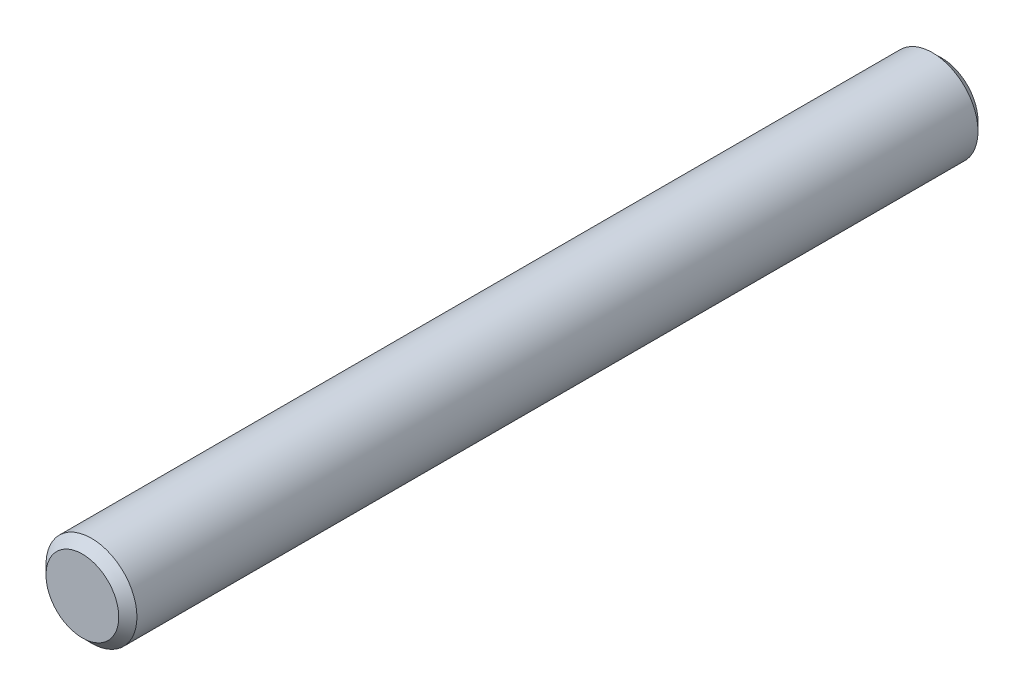
SolidWorks part; units mm, degrees
material "Plain Carbon Steel"
ref_plane "Front" through (0, 0, 0) normal (0, 0, 1) x (1, 0, 0)
ref_plane "Top" through (0, 0, 0) normal (0, 1, 0) x (1, 0, 0)
ref_plane "Right" through (0, 0, 0) normal (1, 0, 0) x (0, 0, -1)
sketch "Sketch1" plane through (0, 0, 0) normal (0, 0, 1) x (1, 0, 0)
  circle A0 centre (0, 0) radius 7.9375
  dimension "Diameter" = 15.875
sketch "Sketch2" plane through (0, 0, 0) normal (1, 0, 0) x (0, 0, -1)
  line L0 (-75, 0) -> (75, 0) construction
  line L1 (-24.2, 7.9375) -> (-24.2, -7.9375) construction
  line L2 (55, 0) -> (-55, 0) construction
  line L3 (24.2, 7.9375) -> (24.2, -7.9375) construction
  line L4 (-75, 7.9375) -> (-75, -7.9375) construction
  line L5 (75, 7.9375) -> (75, -7.9375) construction
  point P3 (-24.2, 0)
  point P8 (0, 0)
  point P9 (24.2, 0)
  point P15 (-75, 0)
  point P18 (75, 0)
  dimension "D1" = 15.875
  dimension "Length" = 150
  dimension "D2" = 50.8
  dimension "D3" = 50.8
sketch "Sketch3" plane through (0, 0, 0) normal (0, 0, 1) x (1, 0, 0)
  circle A0 centre (0, 0) radius 7.9375
  dimension "D1" = 15.875
extrude "Boss-Extrude1" add sketch "Sketch3" along normal mid plane 150
chamfer "Chamfer1" distance 1.5875 angle 45 2 edges at (7.9375, 0, -75) (7.9375, 0, 75)
equation "\"D1@Sketch3\" = \"Diameter@Sketch1\""
equation "\"D1@Boss-Extrude1\" = \"Length@Sketch2\""
equation "\"D1@Chamfer1\" = \"Diameter@Sketch1\" * .1"
equation "\"D1@Sketch2\" = \"Diameter@Sketch1\""
